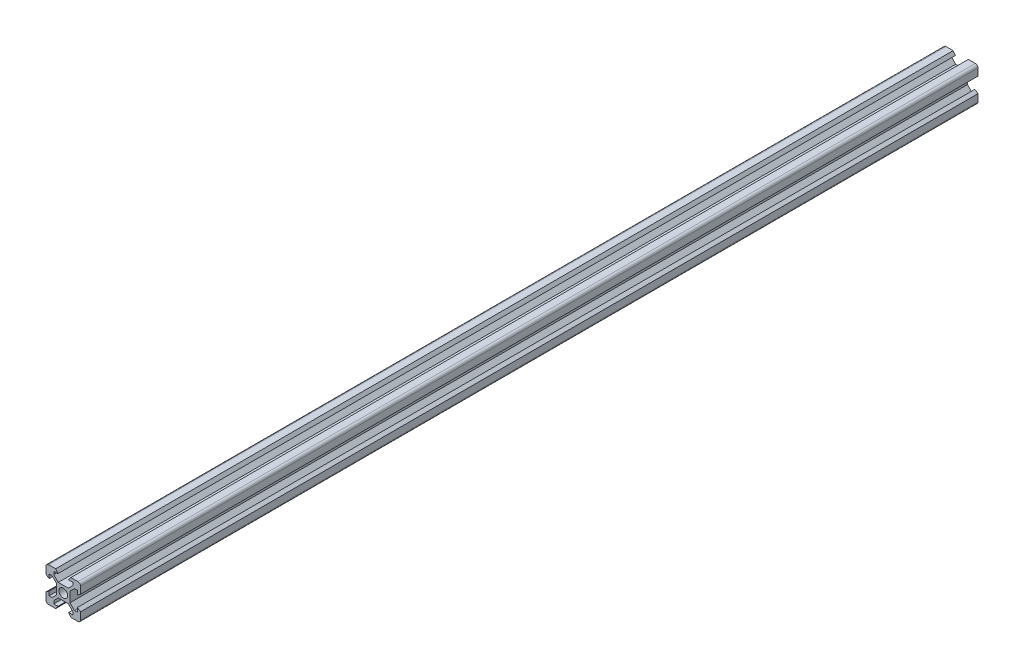
SolidWorks part; units mm, degrees
material "1060 合金"
ref_plane "前视基准面" through (0, 0, 0) normal (0, 0, 1) x (1, 0, 0)
ref_plane "上视基准面" through (0, 0, 0) normal (0, 1, 0) x (1, 0, 0)
ref_plane "右视基准面" through (0, 0, 0) normal (1, 0, 0) x (0, 0, -1)
sketch "草图1" plane through (0, 0, 0) normal (0, 0, 1) x (1, 0, 0)
  line L0 (16.8101, 19.3214) -> (19.4, 21.9114) construction
  line L1 (14.8, 34.8214) -> (18.9, 34.8214)
  line L2 (13.3, 33.3214) -> (13.3, 29.2214)
  line L3 (14.8, 14.8214) -> (18.9, 14.8214)
  line L4 (33.3, 33.3214) -> (33.3, 29.2214)
  line L7 (27.2, 27.7315) -> (29.7899, 30.3214) construction
  line L8 (33.3, 29.2214) -> (31.5, 27.9214)
  line L9 (28.8, 31.3114) -> (26.2101, 28.7214)
  line L10 (31.5, 30.3214) -> (31.5, 27.9214)
  line L11 (29.7899, 30.3214) -> (31.5, 30.3214)
  line L12 (26.2101, 28.7214) -> (28.8, 31.3114) construction
  line L13 (27.2, 27.7315) -> (29.7899, 30.3214)
  line L15 (20.3899, 28.7214) -> (26.2101, 28.7214) construction
  line L18 (18.9, 34.8214) -> (20.2, 33.0214)
  line L19 (27.7, 34.8214) -> (26.4, 33.0214)
  line L20 (26.4, 33.0214) -> (28.8, 33.0214)
  line L21 (28.8, 33.0214) -> (28.8, 31.3114)
  line L22 (26.2101, 28.7214) -> (20.3899, 28.7214)
  line L25 (20.3899, 28.7214) -> (17.8, 31.3114)
  line L26 (17.8, 31.3114) -> (17.8, 33.0214)
  line L27 (17.8, 33.0214) -> (20.2, 33.0214)
  line L28 (27.2, 21.9114) -> (27.2, 27.7315)
  line L29 (29.7899, 19.3214) -> (27.2, 21.9114)
  line L30 (31.5, 19.3214) -> (29.7899, 19.3214)
  line L31 (31.5, 21.7214) -> (31.5, 19.3214)
  line L32 (33.3, 20.4214) -> (31.5, 21.7214)
  line L33 (27.7, 14.8214) -> (26.4, 16.6214)
  line L34 (28.8, 16.6214) -> (26.4, 16.6214)
  line L35 (28.8, 18.3315) -> (28.8, 16.6214)
  line L36 (26.2101, 20.9214) -> (28.8, 18.3315)
  line L37 (20.3899, 20.9214) -> (26.2101, 20.9214)
  line L38 (17.8, 18.3315) -> (20.3899, 20.9214)
  line L39 (17.8, 16.6214) -> (17.8, 18.3315)
  line L40 (20.2, 16.6214) -> (17.8, 16.6214)
  line L41 (18.9, 14.8214) -> (20.2, 16.6214)
  line L42 (13.3, 20.4214) -> (15.1, 21.7214)
  line L43 (15.1, 19.3214) -> (15.1, 21.7214)
  line L44 (16.8101, 19.3214) -> (15.1, 19.3214)
  line L45 (19.4, 21.9114) -> (16.8101, 19.3214)
  line L46 (19.4, 27.7315) -> (19.4, 21.9114)
  line L47 (16.8101, 30.3214) -> (19.4, 27.7315)
  line L48 (15.1, 30.3214) -> (16.8101, 30.3214)
  line L49 (15.1, 27.9214) -> (15.1, 30.3214)
  line L50 (13.3, 29.2214) -> (15.1, 27.9214)
  line L51 (27.7, 34.8214) -> (31.8, 34.8214)
  line L52 (33.3, 20.4214) -> (33.3, 16.3214)
  line L53 (13.3, 20.4214) -> (13.3, 16.3214)
  line L54 (27.7, 14.8214) -> (31.8, 14.8214)
  circle A0 centre (23.3, 24.8214) radius 2.5
  arc A1 (14.8, 34.8214) -> (13.3, 33.3214) centre (14.8, 33.3214) ccw
  arc A2 (33.3, 33.3214) -> (31.8, 34.8214) centre (31.8, 33.3214) ccw
  arc A3 (31.8, 14.8214) -> (33.3, 16.3214) centre (31.8, 16.3214) ccw
  arc A4 (14.8, 14.8214) -> (13.3, 16.3214) centre (14.8, 16.3214) cw
  point P11 (33.3, 34.8214)
  point P18 (33.3, 14.8214)
  dimension "D3" = 5
  dimension "D1" = 1.5
  dimension "D4" = 1.5
  dimension "D5" = 1.5
  dimension "D7" = 1.5
  dimension "D2" = 20
  dimension "D6" = 4
extrude "凸台-拉伸1" add sketch "草图1" along normal blind 520
